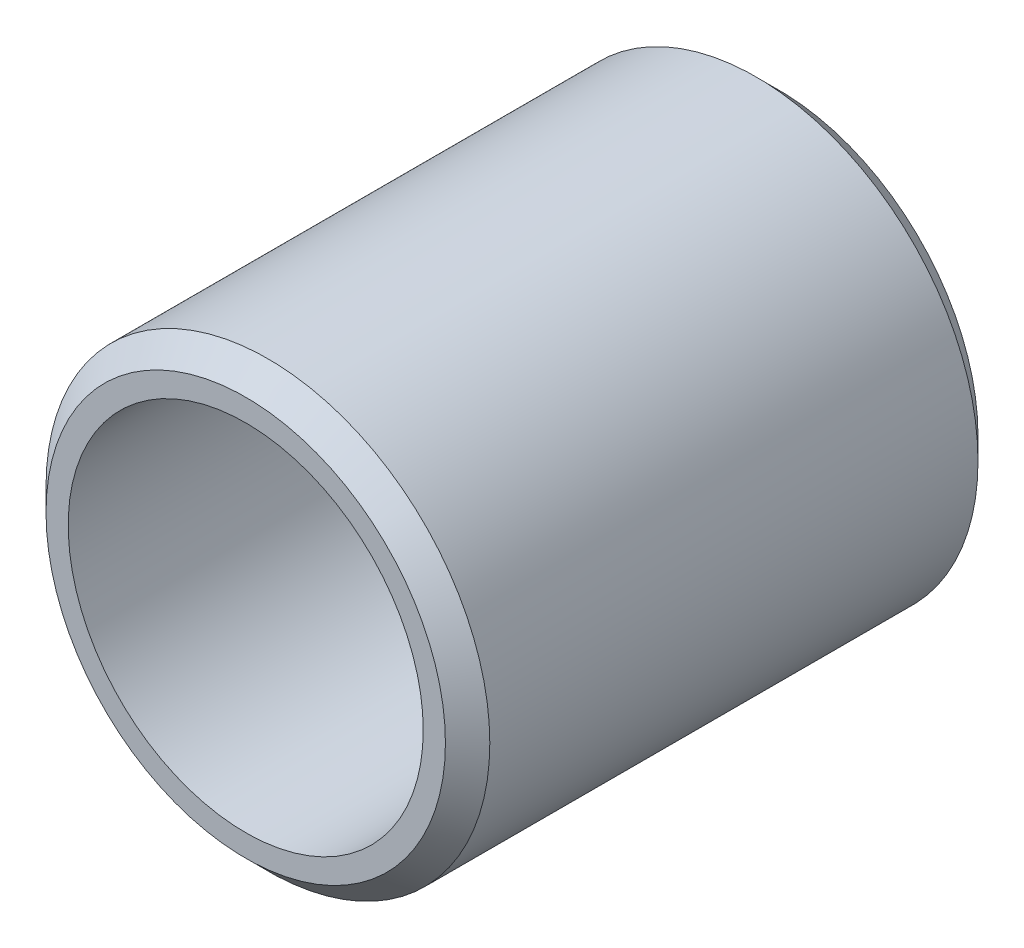
SolidWorks part; units mm, degrees
ref_plane "Спереди" through (0, 0, 0) normal (0, 0, 1) x (1, 0, 0)
ref_plane "Сверху" through (0, 0, 0) normal (0, 1, 0) x (1, 0, 0)
ref_plane "Справа" through (0, 0, 0) normal (1, 0, 0) x (0, 0, -1)
sketch "Эскиз1" plane through (0, 0, 0) normal (0, 0, 1) x (1, 0, 0)
  line L0 (0, 0) -> (12.5314, 0) construction
  circle A0 centre (0, 0) radius 5
  circle A1 centre (0, 0) radius 4
  dimension "D1" = 8
  dimension "D2" = 10
extrude "Бобышка-Вытянуть1" add sketch "Эскиз1" along normal blind 12
chamfer "Фаска1" distance 0.5 angle 45 2 edges at (5, 0, 0) (5, 0, 12)
